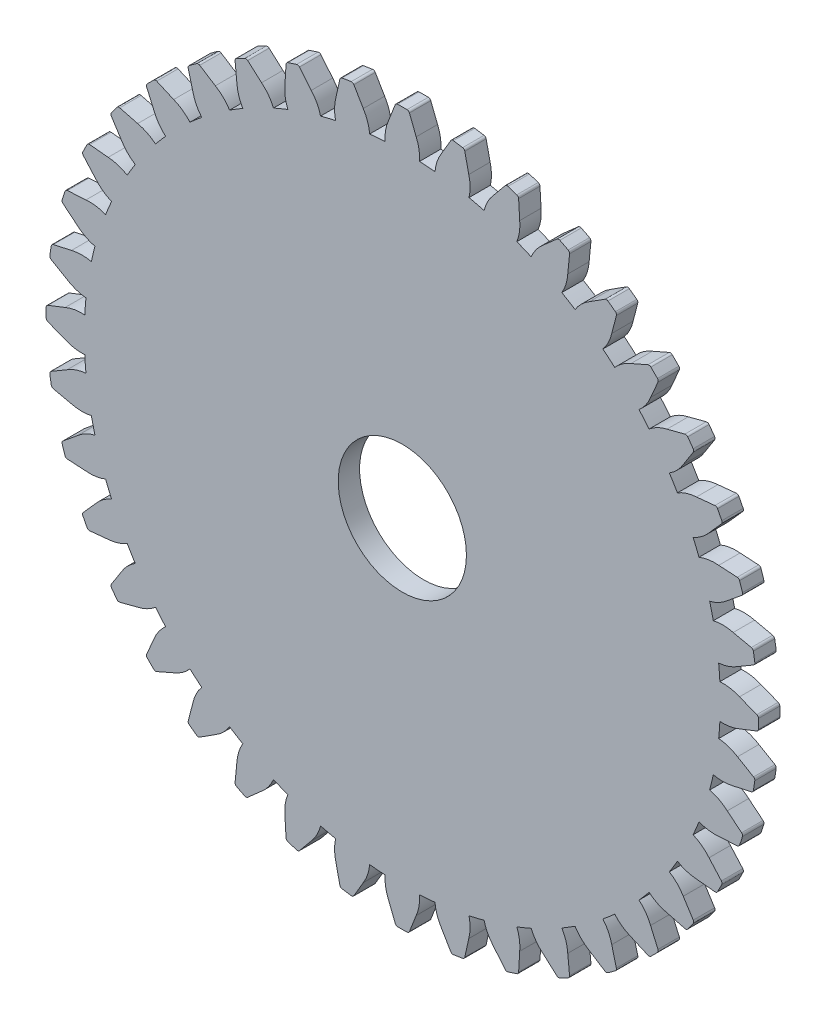
SolidWorks part; units mm, degrees
ref_plane "Front Plane" through (0, 0, 0) normal (0, 0, 1) x (1, 0, 0)
ref_plane "Top Plane" through (0, 0, 0) normal (0, 1, 0) x (1, 0, 0)
ref_plane "Right Plane" through (0, 0, 0) normal (1, 0, 0) x (0, 0, -1)
sketch "Model" plane through (0, 0, 0) normal (0, 0, 1) x (1, 0, 0)
  arc A0 (70.0717, 43.0929) -> (70.0236, 43.8171) centre (40.3497, 41.4817) ccw
  arc A1 (71.9094, 42.7798) -> (70.0717, 43.0929) centre (70.3528, 39.1925) ccw
  arc A2 (73.526, 42.1465) -> (71.9094, 42.7798) centre (-2435.6475, -6360.3539) ccw
  arc A3 (73.6872, 41.4817) -> (73.6844, 41.9176) centre (40.3497, 41.4817) ccw
  arc A4 (73.6844, 41.9176) -> (73.526, 42.1465) centre (73.435, 41.9143) ccw
  arc A5 (70.0236, 39.1463) -> (70.0717, 39.8706) centre (40.3497, 41.4817) ccw
  arc A6 (70.0717, 39.8706) -> (71.9094, 40.1836) centre (70.3528, 43.771) ccw
  arc A7 (71.9094, 40.1836) -> (73.526, 40.8169) centre (-2435.6475, 6443.3173) ccw
  arc A8 (73.6844, 41.0459) -> (73.6872, 41.4817) centre (40.3497, 41.4817) ccw
  arc A9 (73.526, 40.8169) -> (73.6844, 41.0459) centre (73.435, 41.0491) ccw
  arc A10 (69.9578, 38.4235) -> (70.0236, 39.1463) centre (40.3497, 41.4817) ccw
  arc A11 (71.7239, 37.8268) -> (69.9578, 38.4235) centre (69.6253, 34.5272) ccw
  arc A12 (73.2215, 36.9484) -> (71.7239, 37.8268) centre (-3406.6316, -5894.2054) ccw
  arc A13 (73.2768, 36.2666) -> (73.3421, 36.6975) centre (40.3497, 41.4817) ccw
  arc A14 (73.3421, 36.6975) -> (73.2215, 36.9484) centre (73.0954, 36.7333) ccw
  arc A15 (69.2929, 34.5331) -> (69.4537, 35.2409) centre (40.3497, 41.4817) ccw
  arc A16 (69.4537, 35.2409) -> (71.3178, 35.2626) centre (70.3416, 39.0492) ccw
  arc A17 (71.3178, 35.2626) -> (73.0136, 35.6352) centre (-1403.6961, 6751.8314) ccw
  arc A18 (73.2058, 35.8365) -> (73.2768, 36.2666) centre (40.3497, 41.4817) ccw
  arc A19 (73.0136, 35.6352) -> (73.2058, 35.8365) centre (72.96, 35.8788) ccw
  arc A20 (69.1149, 33.8294) -> (69.2929, 34.5331) centre (40.3497, 41.4817) ccw
  arc A21 (70.7659, 32.9638) -> (69.1149, 33.8294) centre (68.177, 30.0331) ccw
  arc A22 (72.1077, 31.8619) -> (70.7659, 32.9638) centre (-4292.7396, -5281.9005) ccw
  arc A23 (72.0556, 31.1799) -> (72.1875, 31.5953) centre (40.3497, 41.4817) ccw
  arc A24 (72.1875, 31.5953) -> (72.1077, 31.8619) centre (71.9494, 31.6692) ccw
  arc A25 (67.8496, 30.0909) -> (68.1191, 30.7649) centre (40.3497, 41.4817) ccw
  arc A26 (68.1191, 30.7649) -> (69.9636, 30.4947) centre (69.5918, 34.3874) ccw
  arc A27 (69.9636, 30.4947) -> (71.6968, 30.5974) centre (-336.1876, 6895.1144) ccw
  arc A28 (71.9182, 30.7662) -> (72.0556, 31.1799) centre (40.3497, 41.4817) ccw
  arc A29 (71.6968, 30.5974) -> (71.9182, 30.7662) centre (71.682, 30.8464) ccw
  arc A30 (67.5636, 29.4238) -> (67.8496, 30.0909) centre (40.3497, 41.4817) ccw
  arc A31 (69.0589, 28.3106) -> (67.5636, 29.4238) centre (66.0434, 25.8209) ccw
  arc A32 (70.2118, 27.0123) -> (69.0589, 28.3106) centre (-5072.1525, -4538.5164) ccw
  arc A33 (70.0536, 26.3468) -> (70.249, 26.7365) centre (40.3497, 41.4817) ccw
  arc A34 (70.249, 26.7365) -> (70.2118, 27.0123) centre (70.0253, 26.8468) ccw
  arc A35 (65.7291, 25.9292) -> (66.1008, 26.5527) centre (40.3497, 41.4817) ccw
  arc A36 (66.1008, 26.5527) -> (67.8803, 25.9973) centre (68.122, 29.9003) ccw
  arc A37 (67.8803, 25.9973) -> (69.6082, 25.8277) centre (740.5926, 6869.6382) ccw
  arc A38 (69.8532, 25.9598) -> (70.0536, 26.3468) centre (40.3497, 41.4817) ccw
  arc A39 (69.6082, 25.8277) -> (69.8532, 25.9598) centre (69.6325, 26.0759) ccw
  arc A40 (65.3423, 25.315) -> (65.7291, 25.9292) centre (40.3497, 41.4817) ccw
  arc A41 (66.645, 23.9816) -> (65.3423, 25.315) centre (63.2772, 21.9943) ccw
  arc A42 (67.5806, 22.519) -> (66.645, 23.9816) centre (-5725.6787, -3682.3574) ccw
  arc A43 (67.3203, 21.8864) -> (67.5742, 22.2407) centre (40.3497, 41.4817) ccw
  arc A44 (67.5742, 22.2407) -> (67.5806, 22.519) centre (67.3706, 22.3847) ccw
  arc A45 (62.9837, 22.1505) -> (63.4483, 22.7082) centre (40.3497, 41.4817) ccw
  arc A46 (63.4483, 22.7082) -> (65.119, 21.8812) centre (65.9683, 25.6984) ccw
  arc A47 (65.119, 21.8812) -> (66.7991, 21.4434) centre (1800.1305, 6676.0302) ccw
  arc A48 (67.0618, 21.5355) -> (67.3203, 21.8864) centre (40.3497, 41.4817) ccw
  arc A49 (66.7991, 21.4434) -> (67.0618, 21.5355) centre (66.862, 21.6847) ccw
  arc A50 (62.5056, 21.6043) -> (62.9837, 22.1505) centre (40.3497, 41.4817) ccw
  arc A51 (63.5837, 20.0836) -> (62.5056, 21.6043) centre (59.9464, 18.6476) ccw
  arc A52 (64.279, 18.4926) -> (63.5837, 20.0836) centre (-6237.2261, -2734.5052) ccw
  arc A53 (63.9229, 17.9086) -> (64.2291, 18.2188) centre (40.3497, 41.4817) ccw
  arc A54 (64.2291, 18.2188) -> (64.279, 18.4926) centre (64.0505, 18.3928) ccw
  arc A55 (59.6809, 18.8478) -> (60.2271, 19.3259) centre (40.3497, 41.4817) ccw
  arc A56 (60.2271, 19.3259) -> (61.7479, 18.2478) centre (63.1839, 21.885) ccw
  arc A57 (61.7479, 18.2478) -> (63.3388, 17.5525) centre (2816.3367, 6319.0575) ccw
  arc A58 (63.6127, 17.6024) -> (63.9229, 17.9086) centre (40.3497, 41.4817) ccw
  arc A59 (63.3388, 17.5525) -> (63.6127, 17.6024) centre (63.4387, 17.781) ccw
  arc A60 (59.1233, 18.3831) -> (59.6809, 18.8478) centre (40.3497, 41.4817) ccw
  arc A61 (59.9502, 16.7124) -> (59.1233, 18.3831) centre (56.1331, 15.8631) ccw
  arc A62 (60.3881, 15.0323) -> (59.9502, 16.7124) centre (-6594.1987, -1718.299) ccw
  arc A63 (59.945, 14.5111) -> (60.296, 14.7696) centre (40.3497, 41.4817) ccw
  arc A64 (60.296, 14.7696) -> (60.3881, 15.0323) centre (60.1468, 14.9694) ccw
  arc A65 (55.9022, 16.1024) -> (56.5164, 16.4891) centre (40.3497, 41.4817) ccw
  arc A66 (56.5164, 16.4891) -> (57.8498, 15.1864) centre (59.8371, 18.5543) ccw
  arc A67 (57.8498, 15.1864) -> (59.3124, 14.2508) centre (3764.1889, 5807.5101) ccw
  arc A68 (59.5907, 14.2572) -> (59.945, 14.5111) centre (40.3497, 41.4817) ccw
  arc A69 (59.3124, 14.2508) -> (59.5907, 14.2572) centre (59.4468, 14.4609) ccw
  arc A70 (55.2787, 15.7307) -> (55.9022, 16.1024) centre (40.3497, 41.4817) ccw
  arc A71 (55.8341, 13.9512) -> (55.2787, 15.7307) centre (51.9311, 13.7095) ccw
  arc A72 (56.0038, 12.2232) -> (55.8341, 13.9512) centre (-6787.8068, -658.7612) ccw
  arc A73 (55.4846, 11.7778) -> (55.8717, 11.9782) centre (40.3497, 41.4817) ccw
  arc A74 (55.8717, 11.9782) -> (56.0038, 12.2232) centre (55.7556, 12.1989) ccw
  arc A75 (51.7405, 13.9819) -> (52.4077, 14.2678) centre (40.3497, 41.4817) ccw
  arc A76 (52.4077, 14.2678) -> (53.5209, 12.7725) centre (56.0106, 15.788) ccw
  arc A77 (53.5209, 12.7725) -> (54.8191, 11.6196) centre (4620.3478, 5153.9839) ccw
  arc A78 (55.095, 11.5825) -> (55.4846, 11.7778) centre (40.3497, 41.4817) ccw
  arc A79 (54.8191, 11.6196) -> (55.095, 11.5825) centre (54.9847, 11.8061) ccw
  arc A80 (51.0666, 13.7123) -> (51.7405, 13.9819) centre (40.3497, 41.4817) ccw
  arc A81 (51.3368, 11.8678) -> (51.0666, 13.7123) centre (47.444, 12.2396) ccw
  arc A82 (51.234, 10.1346) -> (51.3368, 11.8678) centre (-6813.283, 418.019) ccw
  arc A83 (50.6516, 9.7759) -> (51.0652, 9.9133) centre (40.3497, 41.4817) ccw
  arc A84 (51.0652, 9.9133) -> (51.234, 10.1346) centre (50.9851, 10.1494) ccw
  arc A85 (47.2984, 12.5385) -> (48.002, 12.7166) centre (40.3497, 41.4817) ccw
  arc A86 (48.002, 12.7166) -> (48.8676, 11.0655) centre (51.7984, 13.6545) ccw
  arc A87 (48.8676, 11.0655) -> (49.9695, 9.7238) centre (5363.732, 4374.571) ccw
  arc A88 (50.2361, 9.6439) -> (50.6516, 9.7759) centre (40.3497, 41.4817) ccw
  arc A89 (49.9695, 9.7238) -> (50.2361, 9.6439) centre (50.1622, 9.882) ccw
  arc A90 (46.5905, 12.3777) -> (47.2984, 12.5385) centre (40.3497, 41.4817) ccw
  arc A91 (46.5689, 10.5137) -> (46.5905, 12.3777) centre (42.7822, 11.4899) ccw
  arc A92 (46.1962, 8.8179) -> (46.5689, 10.5137) centre (-6670, 1485.5276) ccw
  arc A93 (45.5648, 8.5547) -> (45.9949, 8.6257) centre (40.3497, 41.4817) ccw
  arc A94 (45.9949, 8.6257) -> (46.1962, 8.8179) centre (45.9527, 8.8714) ccw
  arc A95 (42.6851, 11.8079) -> (43.408, 11.8736) centre (40.3497, 41.4817) ccw
  arc A96 (43.408, 11.8736) -> (44.0046, 10.1075) centre (47.3043, 12.2061) ccw
  arc A97 (44.0046, 10.1075) -> (44.883, 8.6099) centre (5976.0368, 3488.463) ccw
  arc A98 (45.1339, 8.4893) -> (45.5648, 8.5547) centre (40.3497, 41.4817) ccw
  arc A99 (44.883, 8.6099) -> (45.1339, 8.4893) centre (45.0981, 8.7361) ccw
  arc A100 (41.9608, 11.7597) -> (42.6851, 11.8079) centre (40.3497, 41.4817) ccw
  arc A101 (41.6478, 9.922) -> (41.9608, 11.7597) centre (38.0605, 11.4786) ccw
  arc A102 (41.0145, 8.3054) -> (41.6478, 9.922) centre (-6361.4859, 2517.4789) ccw
  arc A103 (40.3497, 8.1442) -> (40.7856, 8.1471) centre (40.3497, 41.4817) ccw
  arc A104 (40.7856, 8.1471) -> (41.0145, 8.3054) centre (40.7823, 8.3964) ccw
  arc A105 (38.0143, 11.8079) -> (38.7386, 11.7597) centre (40.3497, 41.4817) ccw
  arc A106 (38.7386, 11.7597) -> (39.0516, 9.922) centre (42.6389, 11.4786) ccw
  arc A107 (39.0516, 9.922) -> (39.6849, 8.3054) centre (6442.1853, 2517.4789) ccw
  arc A108 (39.9138, 8.1471) -> (40.3497, 8.1442) centre (40.3497, 41.4817) ccw
  arc A109 (39.6849, 8.3054) -> (39.9138, 8.1471) centre (39.9171, 8.3964) ccw
  arc A110 (37.2915, 11.8736) -> (38.0143, 11.8079) centre (40.3497, 41.4817) ccw
  arc A111 (36.6948, 10.1075) -> (37.2915, 11.8736) centre (33.3951, 12.2061) ccw
  arc A112 (35.8164, 8.6099) -> (36.6948, 10.1075) centre (-5895.3374, 3488.463) ccw
  arc A113 (35.1346, 8.5547) -> (35.5655, 8.4893) centre (40.3497, 41.4817) ccw
  arc A114 (35.5655, 8.4893) -> (35.8164, 8.6099) centre (35.6013, 8.7361) ccw
  arc A115 (33.4011, 12.5385) -> (34.1089, 12.3777) centre (40.3497, 41.4817) ccw
  arc A116 (34.1089, 12.3777) -> (34.1306, 10.5137) centre (37.9172, 11.4899) ccw
  arc A117 (34.1306, 10.5137) -> (34.5032, 8.8179) centre (6750.6994, 1485.5276) ccw
  arc A118 (34.7045, 8.6257) -> (35.1346, 8.5547) centre (40.3497, 41.4817) ccw
  arc A119 (34.5032, 8.8179) -> (34.7045, 8.6257) centre (34.7467, 8.8714) ccw
  arc A120 (32.6974, 12.7166) -> (33.4011, 12.5385) centre (40.3497, 41.4817) ccw
  arc A121 (31.8318, 11.0655) -> (32.6974, 12.7166) centre (28.901, 13.6545) ccw
  arc A122 (30.7299, 9.7238) -> (31.8318, 11.0655) centre (-5283.0326, 4374.571) ccw
  arc A123 (30.0479, 9.7759) -> (30.4633, 9.6439) centre (40.3497, 41.4817) ccw
  arc A124 (30.4633, 9.6439) -> (30.7299, 9.7238) centre (30.5372, 9.882) ccw
  arc A125 (28.9589, 13.9819) -> (29.6328, 13.7123) centre (40.3497, 41.4817) ccw
  arc A126 (29.6328, 13.7123) -> (29.3627, 11.8678) centre (33.2554, 12.2396) ccw
  arc A127 (29.3627, 11.8678) -> (29.4654, 10.1346) centre (6893.9824, 418.019) ccw
  arc A128 (29.6342, 9.9133) -> (30.0479, 9.7759) centre (40.3497, 41.4817) ccw
  arc A129 (29.4654, 10.1346) -> (29.6342, 9.9133) centre (29.7144, 10.1494) ccw
  arc A130 (28.2917, 14.2678) -> (28.9589, 13.9819) centre (40.3497, 41.4817) ccw
  arc A131 (27.1785, 12.7725) -> (28.2917, 14.2678) centre (24.6889, 15.788) ccw
  arc A132 (25.8803, 11.6196) -> (27.1785, 12.7725) centre (-4539.6484, 5153.9839) ccw
  arc A133 (25.2148, 11.7778) -> (25.6045, 11.5825) centre (40.3497, 41.4817) ccw
  arc A134 (25.6045, 11.5825) -> (25.8803, 11.6196) centre (25.7148, 11.8061) ccw
  arc A135 (24.7972, 16.1024) -> (25.4207, 15.7307) centre (40.3497, 41.4817) ccw
  arc A136 (25.4207, 15.7307) -> (24.8653, 13.9512) centre (28.7683, 13.7095) ccw
  arc A137 (24.8653, 13.9512) -> (24.6957, 12.2232) centre (6868.5062, -658.7612) ccw
  arc A138 (24.8277, 11.9782) -> (25.2148, 11.7778) centre (40.3497, 41.4817) ccw
  arc A139 (24.6957, 12.2232) -> (24.8277, 11.9782) centre (24.9438, 12.1989) ccw
  arc A140 (24.183, 16.4891) -> (24.7972, 16.1024) centre (40.3497, 41.4817) ccw
  arc A141 (22.8496, 15.1864) -> (24.183, 16.4891) centre (20.8623, 18.5543) ccw
  arc A142 (21.387, 14.2508) -> (22.8496, 15.1864) centre (-3683.4895, 5807.5101) ccw
  arc A143 (20.7544, 14.5111) -> (21.1087, 14.2572) centre (40.3497, 41.4817) ccw
  arc A144 (21.1087, 14.2572) -> (21.387, 14.2508) centre (21.2526, 14.4609) ccw
  arc A145 (21.0185, 18.8478) -> (21.5761, 18.3831) centre (40.3497, 41.4817) ccw
  arc A146 (21.5761, 18.3831) -> (20.7492, 16.7124) centre (24.5663, 15.8631) ccw
  arc A147 (20.7492, 16.7124) -> (20.3114, 15.0323) centre (6674.8982, -1718.299) ccw
  arc A148 (20.4035, 14.7696) -> (20.7544, 14.5111) centre (40.3497, 41.4817) ccw
  arc A149 (20.3114, 15.0323) -> (20.4035, 14.7696) centre (20.5527, 14.9694) ccw
  arc A150 (20.4723, 19.3259) -> (21.0185, 18.8478) centre (40.3497, 41.4817) ccw
  arc A151 (18.9515, 18.2478) -> (20.4723, 19.3259) centre (17.5156, 21.885) ccw
  arc A152 (17.3606, 17.5525) -> (18.9515, 18.2478) centre (-2735.6373, 6319.0575) ccw
  arc A153 (16.7765, 17.9086) -> (17.0868, 17.6024) centre (40.3497, 41.4817) ccw
  arc A154 (17.0868, 17.6024) -> (17.3606, 17.5525) centre (17.2608, 17.781) ccw
  arc A155 (17.7158, 22.1505) -> (18.1939, 21.6043) centre (40.3497, 41.4817) ccw
  arc A156 (18.1939, 21.6043) -> (17.1157, 20.0836) centre (20.753, 18.6476) ccw
  arc A157 (17.1157, 20.0836) -> (16.4205, 18.4926) centre (6317.9255, -2734.5052) ccw
  arc A158 (16.4703, 18.2188) -> (16.7765, 17.9086) centre (40.3497, 41.4817) ccw
  arc A159 (16.4205, 18.4926) -> (16.4703, 18.2188) centre (16.649, 18.3928) ccw
  arc A160 (17.2511, 22.7082) -> (17.7158, 22.1505) centre (40.3497, 41.4817) ccw
  arc A161 (15.5804, 21.8812) -> (17.2511, 22.7082) centre (14.7311, 25.6984) ccw
  arc A162 (13.9003, 21.4434) -> (15.5804, 21.8812) centre (-1719.431, 6676.0302) ccw
  arc A163 (13.3791, 21.8864) -> (13.6376, 21.5355) centre (40.3497, 41.4817) ccw
  arc A164 (13.6376, 21.5355) -> (13.9003, 21.4434) centre (13.8374, 21.6847) ccw
  arc A165 (14.9703, 25.9292) -> (15.3571, 25.315) centre (40.3497, 41.4817) ccw
  arc A166 (15.3571, 25.315) -> (14.0544, 23.9816) centre (17.4222, 21.9943) ccw
  arc A167 (14.0544, 23.9816) -> (13.1188, 22.519) centre (5806.3781, -3682.3574) ccw
  arc A168 (13.1252, 22.2407) -> (13.3791, 21.8864) centre (40.3497, 41.4817) ccw
  arc A169 (13.1188, 22.519) -> (13.1252, 22.2407) centre (13.3289, 22.3847) ccw
  arc A170 (14.5987, 26.5527) -> (14.9703, 25.9292) centre (40.3497, 41.4817) ccw
  arc A171 (12.8192, 25.9973) -> (14.5987, 26.5527) centre (12.5774, 29.9003) ccw
  arc A172 (11.0912, 25.8277) -> (12.8192, 25.9973) centre (-659.8932, 6869.6382) ccw
  arc A173 (10.6458, 26.3468) -> (10.8462, 25.9598) centre (40.3497, 41.4817) ccw
  arc A174 (10.8462, 25.9598) -> (11.0912, 25.8277) centre (11.0669, 26.0759) ccw
  arc A175 (12.8499, 30.0909) -> (13.1358, 29.4238) centre (40.3497, 41.4817) ccw
  arc A176 (13.1358, 29.4238) -> (11.6405, 28.3106) centre (14.656, 25.8209) ccw
  arc A177 (11.6405, 28.3106) -> (10.4876, 27.0123) centre (5152.8519, -4538.5164) ccw
  arc A178 (10.4504, 26.7365) -> (10.6458, 26.3468) centre (40.3497, 41.4817) ccw
  arc A179 (10.4876, 27.0123) -> (10.4504, 26.7365) centre (10.6741, 26.8468) ccw
  arc A180 (12.5803, 30.7649) -> (12.8499, 30.0909) centre (40.3497, 41.4817) ccw
  arc A181 (10.7358, 30.4947) -> (12.5803, 30.7649) centre (11.1076, 34.3874) ccw
  arc A182 (9.0026, 30.5974) -> (10.7358, 30.4947) centre (416.887, 6895.1144) ccw
  arc A183 (8.6439, 31.1799) -> (8.7813, 30.7662) centre (40.3497, 41.4817) ccw
  arc A184 (8.7813, 30.7662) -> (9.0026, 30.5974) centre (9.0174, 30.8464) ccw
  arc A185 (11.4065, 34.5331) -> (11.5846, 33.8294) centre (40.3497, 41.4817) ccw
  arc A186 (11.5846, 33.8294) -> (9.9335, 32.9638) centre (12.5224, 30.0331) ccw
  arc A187 (9.9335, 32.9638) -> (8.5917, 31.8619) centre (4373.439, -5281.9005) ccw
  arc A188 (8.5119, 31.5953) -> (8.6439, 31.1799) centre (40.3497, 41.4817) ccw
  arc A189 (8.5917, 31.8619) -> (8.5119, 31.5953) centre (8.75, 31.6692) ccw
  arc A190 (11.2457, 35.2409) -> (11.4065, 34.5331) centre (40.3497, 41.4817) ccw
  arc A191 (9.3816, 35.2626) -> (11.2457, 35.2409) centre (10.3578, 39.0492) ccw
  arc A192 (7.6859, 35.6352) -> (9.3816, 35.2626) centre (1484.3955, 6751.8314) ccw
  arc A193 (7.4226, 36.2666) -> (7.4936, 35.8365) centre (40.3497, 41.4817) ccw
  arc A194 (7.4936, 35.8365) -> (7.6859, 35.6352) centre (7.7394, 35.8788) ccw
  arc A195 (10.6758, 39.1463) -> (10.7416, 38.4235) centre (40.3497, 41.4817) ccw
  arc A196 (10.7416, 38.4235) -> (8.9755, 37.8268) centre (11.0741, 34.5272) ccw
  arc A197 (8.9755, 37.8268) -> (7.4779, 36.9484) centre (3487.331, -5894.2054) ccw
  arc A198 (7.3573, 36.6975) -> (7.4226, 36.2666) centre (40.3497, 41.4817) ccw
  arc A199 (7.4779, 36.9484) -> (7.3573, 36.6975) centre (7.6041, 36.7333) ccw
  arc A200 (10.6277, 39.8706) -> (10.6758, 39.1463) centre (40.3497, 41.4817) ccw
  arc A201 (8.79, 40.1836) -> (10.6277, 39.8706) centre (10.3466, 43.771) ccw
  arc A202 (7.1734, 40.8169) -> (8.79, 40.1836) centre (2516.3469, 6443.3173) ccw
  arc A203 (7.0122, 41.4817) -> (7.0151, 41.0459) centre (40.3497, 41.4817) ccw
  arc A204 (7.0151, 41.0459) -> (7.1734, 40.8169) centre (7.2644, 41.0491) ccw
  arc A205 (10.6758, 43.8171) -> (10.6277, 43.0929) centre (40.3497, 41.4817) ccw
  arc A206 (10.6277, 43.0929) -> (8.79, 42.7798) centre (10.3466, 39.1925) ccw
  arc A207 (8.79, 42.7798) -> (7.1734, 42.1465) centre (2516.3469, -6360.3539) ccw
  arc A208 (7.0151, 41.9176) -> (7.0122, 41.4817) centre (40.3497, 41.4817) ccw
  arc A209 (7.1734, 42.1465) -> (7.0151, 41.9176) centre (7.2644, 41.9143) ccw
  arc A210 (10.7416, 44.54) -> (10.6758, 43.8171) centre (40.3497, 41.4817) ccw
  arc A211 (8.9755, 45.1366) -> (10.7416, 44.54) centre (11.0741, 48.4363) ccw
  arc A212 (7.4779, 46.015) -> (8.9755, 45.1366) centre (3487.331, 5977.1688) ccw
  arc A213 (7.4226, 46.6969) -> (7.3573, 46.2659) centre (40.3497, 41.4817) ccw
  arc A214 (7.3573, 46.2659) -> (7.4779, 46.015) centre (7.6041, 46.2301) ccw
  arc A215 (11.4065, 48.4304) -> (11.2457, 47.7226) centre (40.3497, 41.4817) ccw
  arc A216 (11.2457, 47.7226) -> (9.3816, 47.7009) centre (10.3578, 43.9142) ccw
  arc A217 (9.3816, 47.7009) -> (7.6859, 47.3282) centre (1484.3955, -6668.868) ccw
  arc A218 (7.4936, 47.1269) -> (7.4226, 46.6969) centre (40.3497, 41.4817) ccw
  arc A219 (7.6859, 47.3282) -> (7.4936, 47.1269) centre (7.7394, 47.0847) ccw
  arc A220 (11.5846, 49.1341) -> (11.4065, 48.4304) centre (40.3497, 41.4817) ccw
  arc A221 (9.9335, 49.9996) -> (11.5846, 49.1341) centre (12.5224, 52.9304) ccw
  arc A222 (8.5917, 51.1015) -> (9.9335, 49.9996) centre (4373.439, 5364.864) ccw
  arc A223 (8.6439, 51.7836) -> (8.5119, 51.3682) centre (40.3497, 41.4817) ccw
  arc A224 (8.5119, 51.3682) -> (8.5917, 51.1015) centre (8.75, 51.2942) ccw
  arc A225 (12.8499, 52.8725) -> (12.5803, 52.1986) centre (40.3497, 41.4817) ccw
  arc A226 (12.5803, 52.1986) -> (10.7358, 52.4688) centre (11.1076, 48.576) ccw
  arc A227 (10.7358, 52.4688) -> (9.0026, 52.366) centre (416.887, -6812.151) ccw
  arc A228 (8.7813, 52.1972) -> (8.6439, 51.7836) centre (40.3497, 41.4817) ccw
  arc A229 (9.0026, 52.366) -> (8.7813, 52.1972) centre (9.0174, 52.1171) ccw
  arc A230 (13.1358, 53.5397) -> (12.8499, 52.8725) centre (40.3497, 41.4817) ccw
  arc A231 (11.6405, 54.6529) -> (13.1358, 53.5397) centre (14.656, 57.1426) ccw
  arc A232 (10.4876, 55.9511) -> (11.6405, 54.6529) centre (5152.8519, 4621.4798) ccw
  arc A233 (10.6458, 56.6166) -> (10.4504, 56.227) centre (40.3497, 41.4817) ccw
  arc A234 (10.4504, 56.227) -> (10.4876, 55.9511) centre (10.6741, 56.1167) ccw
  arc A235 (14.9703, 57.0342) -> (14.5987, 56.4108) centre (40.3497, 41.4817) ccw
  arc A236 (14.5987, 56.4108) -> (12.8192, 56.9661) centre (12.5774, 53.0632) ccw
  arc A237 (12.8192, 56.9661) -> (11.0912, 57.1358) centre (-659.8932, -6786.6748) ccw
  arc A238 (10.8462, 57.0037) -> (10.6458, 56.6166) centre (40.3497, 41.4817) ccw
  arc A239 (11.0912, 57.1358) -> (10.8462, 57.0037) centre (11.0669, 56.8876) ccw
  arc A240 (15.3571, 57.6484) -> (14.9703, 57.0342) centre (40.3497, 41.4817) ccw
  arc A241 (14.0544, 58.9819) -> (15.3571, 57.6484) centre (17.4222, 60.9692) ccw
  arc A242 (13.1188, 60.4444) -> (14.0544, 58.9819) centre (5806.3781, 3765.3209) ccw
  arc A243 (13.3791, 61.077) -> (13.1252, 60.7227) centre (40.3497, 41.4817) ccw
  arc A244 (13.1252, 60.7227) -> (13.1188, 60.4444) centre (13.3289, 60.5788) ccw
  arc A245 (17.7158, 60.813) -> (17.2511, 60.2553) centre (40.3497, 41.4817) ccw
  arc A246 (17.2511, 60.2553) -> (15.5804, 61.0822) centre (14.7311, 57.2651) ccw
  arc A247 (15.5804, 61.0822) -> (13.9003, 61.5201) centre (-1719.431, -6593.0667) ccw
  arc A248 (13.6376, 61.428) -> (13.3791, 61.077) centre (40.3497, 41.4817) ccw
  arc A249 (13.9003, 61.5201) -> (13.6376, 61.428) centre (13.8374, 61.2788) ccw
  arc A250 (18.1939, 61.3591) -> (17.7158, 60.813) centre (40.3497, 41.4817) ccw
  arc A251 (17.1157, 62.8799) -> (18.1939, 61.3591) centre (20.753, 64.3159) ccw
  arc A252 (16.4205, 64.4708) -> (17.1157, 62.8799) centre (6317.9255, 2817.4687) ccw
  arc A253 (16.7765, 65.0549) -> (16.4703, 64.7447) centre (40.3497, 41.4817) ccw
  arc A254 (16.4703, 64.7447) -> (16.4205, 64.4708) centre (16.649, 64.5707) ccw
  arc A255 (21.0185, 64.1157) -> (20.4723, 63.6376) centre (40.3497, 41.4817) ccw
  arc A256 (20.4723, 63.6376) -> (18.9515, 64.7157) centre (17.5156, 61.0784) ccw
  arc A257 (18.9515, 64.7157) -> (17.3606, 65.411) centre (-2735.6373, -6236.0941) ccw
  arc A258 (17.0868, 65.3611) -> (16.7765, 65.0549) centre (40.3497, 41.4817) ccw
  arc A259 (17.3606, 65.411) -> (17.0868, 65.3611) centre (17.2608, 65.1825) ccw
  arc A260 (21.5761, 64.5803) -> (21.0185, 64.1157) centre (40.3497, 41.4817) ccw
  arc A261 (20.7492, 66.251) -> (21.5761, 64.5803) centre (24.5663, 67.1003) ccw
  arc A262 (20.3114, 67.9312) -> (20.7492, 66.251) centre (6674.8982, 1801.2625) ccw
  arc A263 (20.7544, 68.4523) -> (20.4035, 68.1938) centre (40.3497, 41.4817) ccw
  arc A264 (20.4035, 68.1938) -> (20.3114, 67.9312) centre (20.5527, 67.994) ccw
  arc A265 (24.7972, 66.8611) -> (24.183, 66.4743) centre (40.3497, 41.4817) ccw
  arc A266 (24.183, 66.4743) -> (22.8496, 67.7771) centre (20.8623, 64.4092) ccw
  arc A267 (22.8496, 67.7771) -> (21.387, 68.7127) centre (-3683.4895, -5724.5466) ccw
  arc A268 (21.1087, 68.7062) -> (20.7544, 68.4523) centre (40.3497, 41.4817) ccw
  arc A269 (21.387, 68.7127) -> (21.1087, 68.7062) centre (21.2526, 68.5026) ccw
  arc A270 (25.4207, 67.2328) -> (24.7972, 66.8611) centre (40.3497, 41.4817) ccw
  arc A271 (24.8653, 69.0123) -> (25.4207, 67.2328) centre (28.7683, 69.254) ccw
  arc A272 (24.6957, 70.7402) -> (24.8653, 69.0123) centre (6868.5062, 741.7246) ccw
  arc A273 (25.2148, 71.1857) -> (24.8277, 70.9852) centre (40.3497, 41.4817) ccw
  arc A274 (24.8277, 70.9852) -> (24.6957, 70.7402) centre (24.9438, 70.7646) ccw
  arc A275 (28.9589, 68.9816) -> (28.2917, 68.6957) centre (40.3497, 41.4817) ccw
  arc A276 (28.2917, 68.6957) -> (27.1785, 70.1909) centre (24.6889, 67.1754) ccw
  arc A277 (27.1785, 70.1909) -> (25.8803, 71.3438) centre (-4539.6484, -5071.0205) ccw
  arc A278 (25.6045, 71.381) -> (25.2148, 71.1857) centre (40.3497, 41.4817) ccw
  arc A279 (25.8803, 71.3438) -> (25.6045, 71.381) centre (25.7148, 71.1574) ccw
  arc A280 (29.6328, 69.2512) -> (28.9589, 68.9816) centre (40.3497, 41.4817) ccw
  arc A281 (29.3627, 71.0956) -> (29.6328, 69.2512) centre (33.2554, 70.7238) ccw
  arc A282 (29.4654, 72.8288) -> (29.3627, 71.0956) centre (6893.9824, -335.0555) ccw
  arc A283 (30.0479, 73.1876) -> (29.6342, 73.0502) centre (40.3497, 41.4817) ccw
  arc A284 (29.6342, 73.0502) -> (29.4654, 72.8288) centre (29.7144, 72.814) ccw
  arc A285 (33.4011, 70.4249) -> (32.6974, 70.2469) centre (40.3497, 41.4817) ccw
  arc A286 (32.6974, 70.2469) -> (31.8318, 71.8979) centre (28.901, 69.309) ccw
  arc A287 (31.8318, 71.8979) -> (30.7299, 73.2397) centre (-5283.0326, -4291.6075) ccw
  arc A288 (30.4633, 73.3196) -> (30.0479, 73.1876) centre (40.3497, 41.4817) ccw
  arc A289 (30.7299, 73.2397) -> (30.4633, 73.3196) centre (30.5372, 73.0814) ccw
  arc A290 (34.1089, 70.5858) -> (33.4011, 70.4249) centre (40.3497, 41.4817) ccw
  arc A291 (34.1306, 72.4498) -> (34.1089, 70.5858) centre (37.9172, 71.4736) ccw
  arc A292 (34.5032, 74.1456) -> (34.1306, 72.4498) centre (6750.6994, -1402.5641) ccw
  arc A293 (35.1346, 74.4088) -> (34.7045, 74.3378) centre (40.3497, 41.4817) ccw
  arc A294 (34.7045, 74.3378) -> (34.5032, 74.1456) centre (34.7467, 74.092) ccw
  arc A295 (38.0143, 71.1556) -> (37.2915, 71.0898) centre (40.3497, 41.4817) ccw
  arc A296 (37.2915, 71.0898) -> (36.6948, 72.8559) centre (33.3951, 70.7574) ccw
  arc A297 (36.6948, 72.8559) -> (35.8164, 74.3536) centre (-5895.3374, -3405.4996) ccw
  arc A298 (35.5655, 74.4742) -> (35.1346, 74.4088) centre (40.3497, 41.4817) ccw
  arc A299 (35.8164, 74.3536) -> (35.5655, 74.4742) centre (35.6013, 74.2274) ccw
  arc A300 (38.7386, 71.2037) -> (38.0143, 71.1556) centre (40.3497, 41.4817) ccw
  arc A301 (39.0516, 73.0414) -> (38.7386, 71.2037) centre (42.6389, 71.4849) ccw
  arc A302 (39.6849, 74.658) -> (39.0516, 73.0414) centre (6442.1853, -2434.5155) ccw
  arc A303 (40.3497, 74.8192) -> (39.9138, 74.8164) centre (40.3497, 41.4817) ccw
  arc A304 (39.9138, 74.8164) -> (39.6849, 74.658) centre (39.9171, 74.567) ccw
  arc A305 (42.6851, 71.1556) -> (41.9608, 71.2037) centre (40.3497, 41.4817) ccw
  arc A306 (41.9608, 71.2037) -> (41.6478, 73.0414) centre (38.0605, 71.4849) ccw
  arc A307 (41.6478, 73.0414) -> (41.0145, 74.658) centre (-6361.4859, -2434.5155) ccw
  arc A308 (40.7856, 74.8164) -> (40.3497, 74.8192) centre (40.3497, 41.4817) ccw
  arc A309 (41.0145, 74.658) -> (40.7856, 74.8164) centre (40.7823, 74.567) ccw
  arc A310 (43.408, 71.0898) -> (42.6851, 71.1556) centre (40.3497, 41.4817) ccw
  arc A311 (44.0046, 72.8559) -> (43.408, 71.0898) centre (47.3043, 70.7574) ccw
  arc A312 (44.883, 74.3536) -> (44.0046, 72.8559) centre (5976.0368, -3405.4996) ccw
  arc A313 (45.5648, 74.4088) -> (45.1339, 74.4742) centre (40.3497, 41.4817) ccw
  arc A314 (45.1339, 74.4742) -> (44.883, 74.3536) centre (45.0981, 74.2274) ccw
  arc A315 (47.2984, 70.4249) -> (46.5905, 70.5858) centre (40.3497, 41.4817) ccw
  arc A316 (46.5905, 70.5858) -> (46.5689, 72.4498) centre (42.7822, 71.4736) ccw
  arc A317 (46.5689, 72.4498) -> (46.1962, 74.1456) centre (-6670, -1402.5641) ccw
  arc A318 (45.9949, 74.3378) -> (45.5648, 74.4088) centre (40.3497, 41.4817) ccw
  arc A319 (46.1962, 74.1456) -> (45.9949, 74.3378) centre (45.9527, 74.092) ccw
  arc A320 (48.002, 70.2469) -> (47.2984, 70.4249) centre (40.3497, 41.4817) ccw
  arc A321 (48.8676, 71.8979) -> (48.002, 70.2469) centre (51.7984, 69.309) ccw
  arc A322 (49.9695, 73.2397) -> (48.8676, 71.8979) centre (5363.732, -4291.6075) ccw
  arc A323 (50.6516, 73.1876) -> (50.2361, 73.3196) centre (40.3497, 41.4817) ccw
  arc A324 (50.2361, 73.3196) -> (49.9695, 73.2397) centre (50.1622, 73.0814) ccw
  arc A325 (51.7405, 68.9816) -> (51.0666, 69.2512) centre (40.3497, 41.4817) ccw
  arc A326 (51.0666, 69.2512) -> (51.3368, 71.0956) centre (47.444, 70.7238) ccw
  arc A327 (51.3368, 71.0956) -> (51.234, 72.8288) centre (-6813.283, -335.0555) ccw
  arc A328 (51.0652, 73.0502) -> (50.6516, 73.1876) centre (40.3497, 41.4817) ccw
  arc A329 (51.234, 72.8288) -> (51.0652, 73.0502) centre (50.9851, 72.814) ccw
  arc A330 (52.4077, 68.6957) -> (51.7405, 68.9816) centre (40.3497, 41.4817) ccw
  arc A331 (53.5209, 70.1909) -> (52.4077, 68.6957) centre (56.0106, 67.1754) ccw
  arc A332 (54.8191, 71.3438) -> (53.5209, 70.1909) centre (4620.3478, -5071.0205) ccw
  arc A333 (55.4846, 71.1857) -> (55.095, 71.381) centre (40.3497, 41.4817) ccw
  arc A334 (55.095, 71.381) -> (54.8191, 71.3438) centre (54.9847, 71.1574) ccw
  arc A335 (55.9022, 66.8611) -> (55.2787, 67.2328) centre (40.3497, 41.4817) ccw
  arc A336 (55.2787, 67.2328) -> (55.8341, 69.0123) centre (51.9311, 69.254) ccw
  arc A337 (55.8341, 69.0123) -> (56.0038, 70.7402) centre (-6787.8068, 741.7246) ccw
  arc A338 (55.8717, 70.9852) -> (55.4846, 71.1857) centre (40.3497, 41.4817) ccw
  arc A339 (56.0038, 70.7402) -> (55.8717, 70.9852) centre (55.7556, 70.7646) ccw
  arc A340 (56.5164, 66.4743) -> (55.9022, 66.8611) centre (40.3497, 41.4817) ccw
  arc A341 (57.8498, 67.7771) -> (56.5164, 66.4743) centre (59.8371, 64.4092) ccw
  arc A342 (59.3124, 68.7127) -> (57.8498, 67.7771) centre (3764.1889, -5724.5466) ccw
  arc A343 (59.945, 68.4523) -> (59.5907, 68.7062) centre (40.3497, 41.4817) ccw
  arc A344 (59.5907, 68.7062) -> (59.3124, 68.7127) centre (59.4468, 68.5026) ccw
  arc A345 (59.6809, 64.1157) -> (59.1233, 64.5803) centre (40.3497, 41.4817) ccw
  arc A346 (59.1233, 64.5803) -> (59.9502, 66.251) centre (56.1331, 67.1003) ccw
  arc A347 (59.9502, 66.251) -> (60.3881, 67.9312) centre (-6594.1987, 1801.2625) ccw
  arc A348 (60.296, 68.1938) -> (59.945, 68.4523) centre (40.3497, 41.4817) ccw
  arc A349 (60.3881, 67.9312) -> (60.296, 68.1938) centre (60.1468, 67.994) ccw
  arc A350 (60.2271, 63.6376) -> (59.6809, 64.1157) centre (40.3497, 41.4817) ccw
  arc A351 (61.7479, 64.7157) -> (60.2271, 63.6376) centre (63.1839, 61.0784) ccw
  arc A352 (63.3388, 65.411) -> (61.7479, 64.7157) centre (2816.3367, -6236.0941) ccw
  arc A353 (63.9229, 65.0549) -> (63.6127, 65.3611) centre (40.3497, 41.4817) ccw
  arc A354 (63.6127, 65.3611) -> (63.3388, 65.411) centre (63.4387, 65.1825) ccw
  arc A355 (62.9837, 60.813) -> (62.5056, 61.3591) centre (40.3497, 41.4817) ccw
  arc A356 (62.5056, 61.3591) -> (63.5837, 62.8799) centre (59.9464, 64.3159) ccw
  arc A357 (63.5837, 62.8799) -> (64.279, 64.4708) centre (-6237.2261, 2817.4687) ccw
  arc A358 (64.2291, 64.7447) -> (63.9229, 65.0549) centre (40.3497, 41.4817) ccw
  arc A359 (64.279, 64.4708) -> (64.2291, 64.7447) centre (64.0505, 64.5707) ccw
  arc A360 (63.4483, 60.2553) -> (62.9837, 60.813) centre (40.3497, 41.4817) ccw
  arc A361 (65.119, 61.0822) -> (63.4483, 60.2553) centre (65.9683, 57.2651) ccw
  arc A362 (66.7991, 61.5201) -> (65.119, 61.0822) centre (1800.1305, -6593.0667) ccw
  arc A363 (67.3203, 61.077) -> (67.0618, 61.428) centre (40.3497, 41.4817) ccw
  arc A364 (67.0618, 61.428) -> (66.7991, 61.5201) centre (66.862, 61.2788) ccw
  arc A365 (65.7291, 57.0342) -> (65.3423, 57.6484) centre (40.3497, 41.4817) ccw
  arc A366 (65.3423, 57.6484) -> (66.645, 58.9819) centre (63.2772, 60.9692) ccw
  arc A367 (66.645, 58.9819) -> (67.5806, 60.4444) centre (-5725.6787, 3765.3209) ccw
  arc A368 (67.5742, 60.7227) -> (67.3203, 61.077) centre (40.3497, 41.4817) ccw
  arc A369 (67.5806, 60.4444) -> (67.5742, 60.7227) centre (67.3706, 60.5788) ccw
  arc A370 (66.1008, 56.4108) -> (65.7291, 57.0342) centre (40.3497, 41.4817) ccw
  arc A371 (67.8803, 56.9661) -> (66.1008, 56.4108) centre (68.122, 53.0632) ccw
  arc A372 (69.6082, 57.1358) -> (67.8803, 56.9661) centre (740.5926, -6786.6748) ccw
  arc A373 (70.0536, 56.6166) -> (69.8532, 57.0037) centre (40.3497, 41.4817) ccw
  arc A374 (69.8532, 57.0037) -> (69.6082, 57.1358) centre (69.6325, 56.8876) ccw
  arc A375 (67.8496, 52.8725) -> (67.5636, 53.5397) centre (40.3497, 41.4817) ccw
  arc A376 (67.5636, 53.5397) -> (69.0589, 54.6529) centre (66.0434, 57.1426) ccw
  arc A377 (69.0589, 54.6529) -> (70.2118, 55.9511) centre (-5072.1525, 4621.4798) ccw
  arc A378 (70.249, 56.227) -> (70.0536, 56.6166) centre (40.3497, 41.4817) ccw
  arc A379 (70.2118, 55.9511) -> (70.249, 56.227) centre (70.0253, 56.1167) ccw
  arc A380 (68.1191, 52.1986) -> (67.8496, 52.8725) centre (40.3497, 41.4817) ccw
  arc A381 (69.9636, 52.4688) -> (68.1191, 52.1986) centre (69.5918, 48.576) ccw
  arc A382 (71.6968, 52.366) -> (69.9636, 52.4688) centre (-336.1876, -6812.151) ccw
  arc A383 (72.0556, 51.7836) -> (71.9182, 52.1972) centre (40.3497, 41.4817) ccw
  arc A384 (71.9182, 52.1972) -> (71.6968, 52.366) centre (71.682, 52.1171) ccw
  arc A385 (69.2929, 48.4304) -> (69.1149, 49.1341) centre (40.3497, 41.4817) ccw
  arc A386 (69.1149, 49.1341) -> (70.7659, 49.9996) centre (68.177, 52.9304) ccw
  arc A387 (70.7659, 49.9996) -> (72.1077, 51.1015) centre (-4292.7396, 5364.864) ccw
  arc A388 (72.1875, 51.3682) -> (72.0556, 51.7836) centre (40.3497, 41.4817) ccw
  arc A389 (72.1077, 51.1015) -> (72.1875, 51.3682) centre (71.9494, 51.2942) ccw
  arc A390 (69.4537, 47.7226) -> (69.2929, 48.4304) centre (40.3497, 41.4817) ccw
  arc A391 (71.3178, 47.7009) -> (69.4537, 47.7226) centre (70.3416, 43.9142) ccw
  arc A392 (73.0136, 47.3282) -> (71.3178, 47.7009) centre (-1403.6961, -6668.868) ccw
  arc A393 (73.2768, 46.6969) -> (73.2058, 47.1269) centre (40.3497, 41.4817) ccw
  arc A394 (73.2058, 47.1269) -> (73.0136, 47.3282) centre (72.96, 47.0847) ccw
  arc A395 (70.0236, 43.8171) -> (69.9578, 44.54) centre (40.3497, 41.4817) ccw
  arc A396 (69.9578, 44.54) -> (71.7239, 45.1366) centre (69.6253, 48.4363) ccw
  arc A397 (71.7239, 45.1366) -> (73.2215, 46.015) centre (-3406.6316, 5977.1688) ccw
  arc A398 (73.3421, 46.2659) -> (73.2768, 46.6969) centre (40.3497, 41.4817) ccw
  arc A399 (73.2215, 46.015) -> (73.3421, 46.2659) centre (73.0954, 46.2301) ccw
  circle A400 centre (40.3497, 41.4817) radius 6
  dimension "D1" = 12
extrude "Boss-Extrude1" add sketch "Model" along normal blind 2
